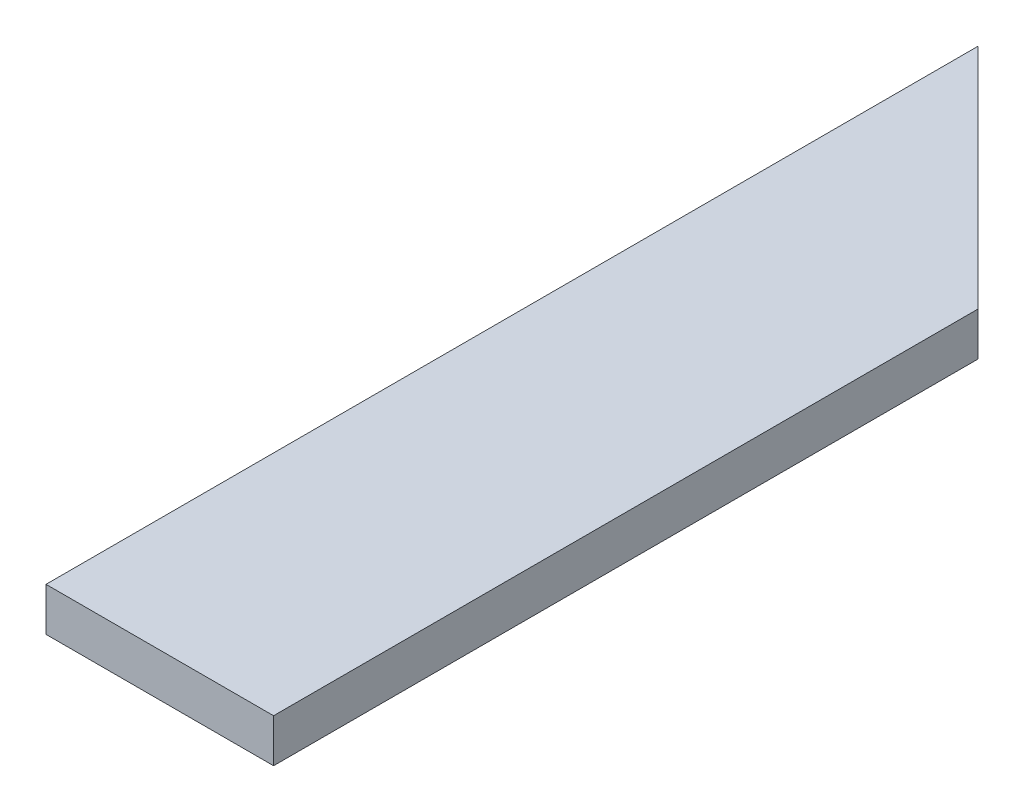
SolidWorks part; units mm, degrees
ref_plane "前视基准面" through (0, 0, 0) normal (0, 0, 1) x (1, 0, 0)
ref_plane "上视基准面" through (0, 0, 0) normal (0, 1, 0) x (1, 0, 0)
ref_plane "右视基准面" through (0, 0, 0) normal (1, 0, 0) x (0, 0, -1)
sketch "草图1" plane through (0, 0, 0) normal (0, 1, 0) x (1, 0, 0)
  line L1 (0, 0) -> (0, 42)
  line L5 (0, 0) -> (0, -130)
  line L6 (42, 0) -> (42, -130)
  line L7 (0, -130) -> (42, -130)
  line L8 (0, 42) -> (42, 0)
extrude "凸台-拉伸1" add sketch "草图1" along normal blind 8
